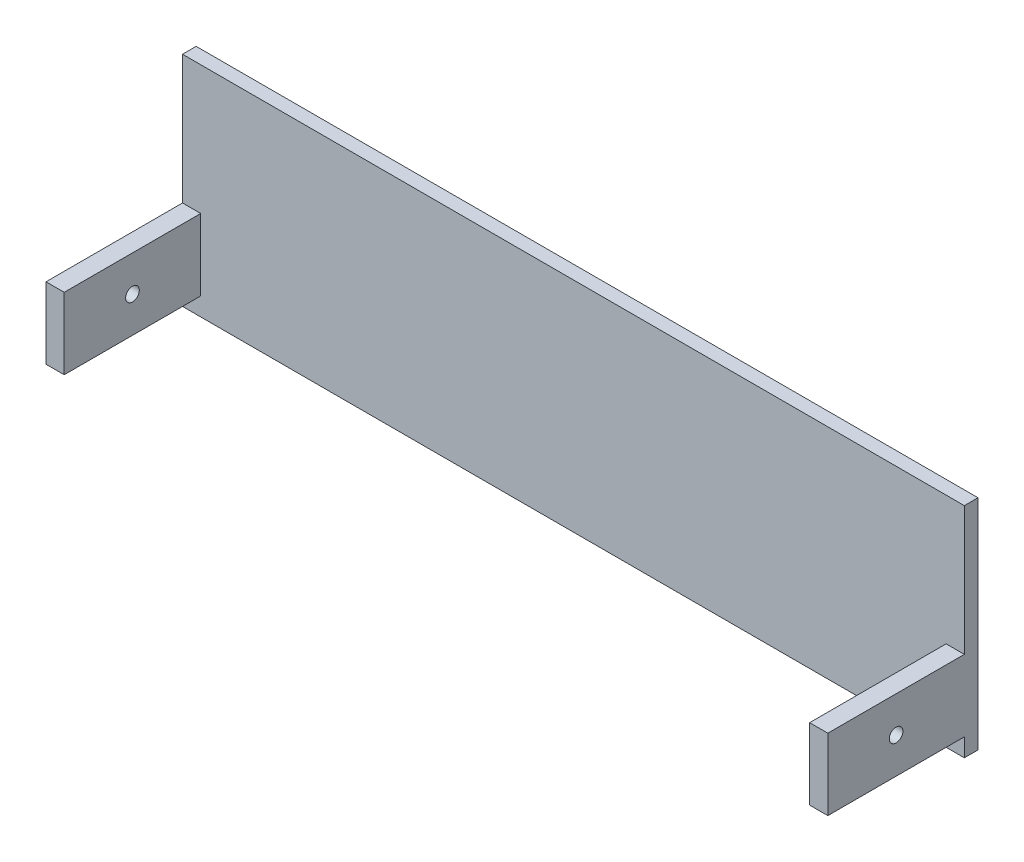
SolidWorks part; units mm, degrees
ref_plane "Alzado" through (0, 0, 0) normal (0, 0, 1) x (1, 0, 0)
ref_plane "Planta" through (0, 0, 0) normal (0, 1, 0) x (1, 0, 0)
ref_plane "Vista lateral" through (0, 0, 0) normal (1, 0, 0) x (0, 0, -1)
sketch "Croquis1" plane through (0, 0, 0) normal (0, 0, 1) x (1, 0, 0)
  line L1 (0, 0) -> (-171.8, 0)
  line L2 (0, 0) -> (0, 48)
  line L3 (0, 48) -> (-171.8, 48)
  line L4 (-171.8, 0) -> (-171.8, 48)
  dimension "D1" = 171.8
  dimension "D2" = 48
extrude "Saliente-Extruir1" add sketch "Croquis1" along normal blind 3
sketch "Croquis2" plane through (0, 0, 3) normal (0, 0, 1) x (1, 0, 0)
  line L0 (-171.8, 48) -> (-171.8, 0) construction
  line L1 (-171.8, 4) -> (-167.8, 4)
  line L2 (-171.8, 4) -> (-171.8, 48)
  line L3 (-171.8, 48) -> (-167.8, 48)
  line L4 (-167.8, 4) -> (-167.8, 48)
  line L5 (0, 48) -> (-171.8, 48) construction
  line L6 (-171.8, 0) -> (0, 0) construction
  line L7 (-85.9, 48) -> (-85.9, 0) construction
  line L8 (0, 48) -> (-4, 48)
  line L9 (-4, 4) -> (-4, 48)
  line L10 (0, 4) -> (-4, 4)
  line L11 (0, 4) -> (0, 48)
  dimension "D1" = 4
  dimension "D2" = 4
extrude "Saliente-Extruir2" add sketch "Croquis2" along normal blind 30
sketch "Croquis3" plane through (-171.8, 0, 0) normal (-1, 0, 0) x (0, 0, 1)
  line L0 (3, 4) -> (3, 48) construction
  line L2 (33, 48) -> (3, 48)
  line L3 (33, 48) -> (33, 19.6959)
  line L4 (33, 19.6959) -> (3, 19.6959)
  line L5 (3, 48) -> (3, 19.6959)
extrude "Cortar-Extruir1" cut sketch "Croquis3" against normal up to vertex
sketch "Croquis4" plane through (-171.8, 0, 0) normal (-1, 0, 0) x (0, 0, 1)
  line L0 (18, 19.6959) -> (18, 4) construction
  line L1 (3, 19.6959) -> (33, 19.6959) construction
  line L2 (33, 4) -> (3, 4) construction
  circle A0 centre (18, 11.8479) radius 1.5
  point P8 (0, 0)
  dimension "D1" = 3
extrude "Cortar-Extruir2" cut sketch "Croquis4" against normal up to vertex
